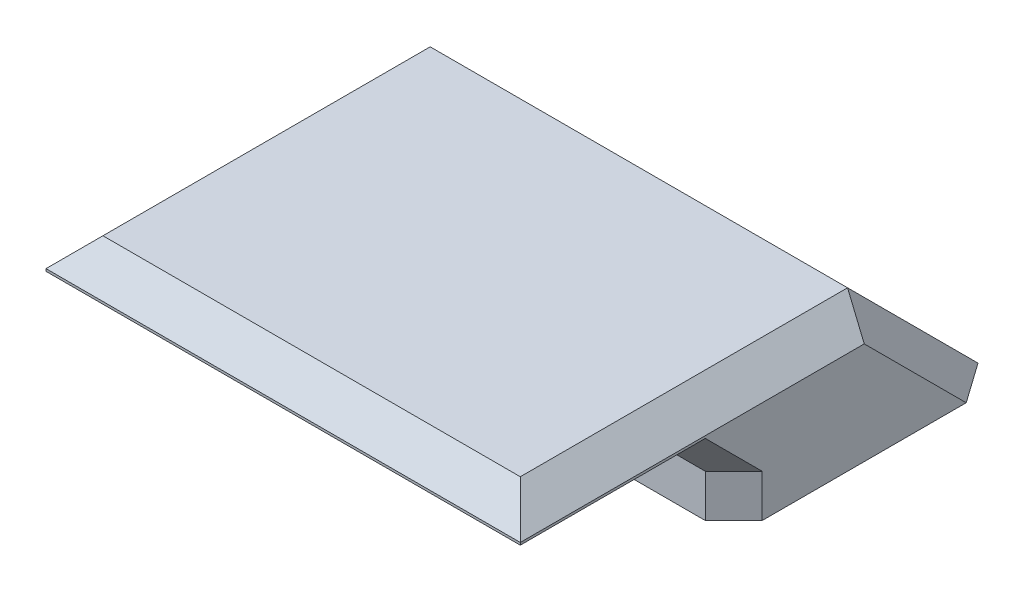
SolidWorks part; units mm, degrees
ref_plane "前视基准面" through (0, 0, 0) normal (0, 0, 1) x (1, 0, 0)
ref_plane "上视基准面" through (0, 0, 0) normal (0, 1, 0) x (1, 0, 0)
ref_plane "右视基准面" through (0, 0, 0) normal (1, 0, 0) x (0, 0, -1)
sketch "草图1" plane through (0, 0, 0) normal (0, 1, 0) x (1, 0, 0)
  line L0 (-10, 0) -> (10, 0) construction
  line L1 (-10, 3) -> (10, 3)
  line L2 (-10, 3) -> (-10, -3)
  line L3 (-10, -3) -> (10, -3)
  line L4 (10, 3) -> (10, -3)
  line L5 (-10, 3) -> (10, -3) construction
  line L6 (-10, -3) -> (10, 3) construction
  line L7 (0, 3) -> (0, -3) construction
  circle A0 centre (-7, 0) radius 1.4
  circle A1 centre (7, 0) radius 1.4
  point P0 (0, 0)
  dimension "D3" = 2.8
  dimension "D1" = 6
  dimension "D2" = 20
  dimension "D4" = 3
extrude "凸台-拉伸1" add sketch "草图1" along normal blind 3
sketch "草图2" plane through (0, 3, 0) normal (0, 1, 0) x (1, 0, 0)
  line L0 (10, -3) -> (10, 3) construction
  line L1 (-10, 3) -> (10, 3)
  line L2 (-10, 3) -> (-10, -12)
  line L3 (-10, -12) -> (10, -12)
  line L4 (10, 3) -> (10, -12)
  dimension "D1" = 15
extrude "凸台-拉伸2" add sketch "草图2" along normal blind 2.5
sketch "草图3" plane through (-10, 0, 0) normal (-1, 0, 0) x (0, 0, 1)
  line L0 (-3, 5.5) -> (-8.5, 0)
  line L1 (-8.5, 0) -> (-3, 0)
  line L2 (-3, 5.5) -> (-3, 0) construction
  line L3 (-3, 5.5) -> (-3, 0)
extrude "凸台-拉伸3" add sketch "草图3" against normal up to vertex (20 mm away) contours L0 L1 L3
chamfer "倒角1" distance 1.2 angle 45 11 edges at (10, 1.5, 3) (-10, 1.5, 3) (10, 3, 7.5) (0, 3, 3) (-10, 3, 7.5) (0, 3, 12) (-10, 2.75, -5.75) (-10, 5.5, 4.5) (0, 5.5, 12) (10, 2.75, -5.75) (10, 5.5, 4.5)
